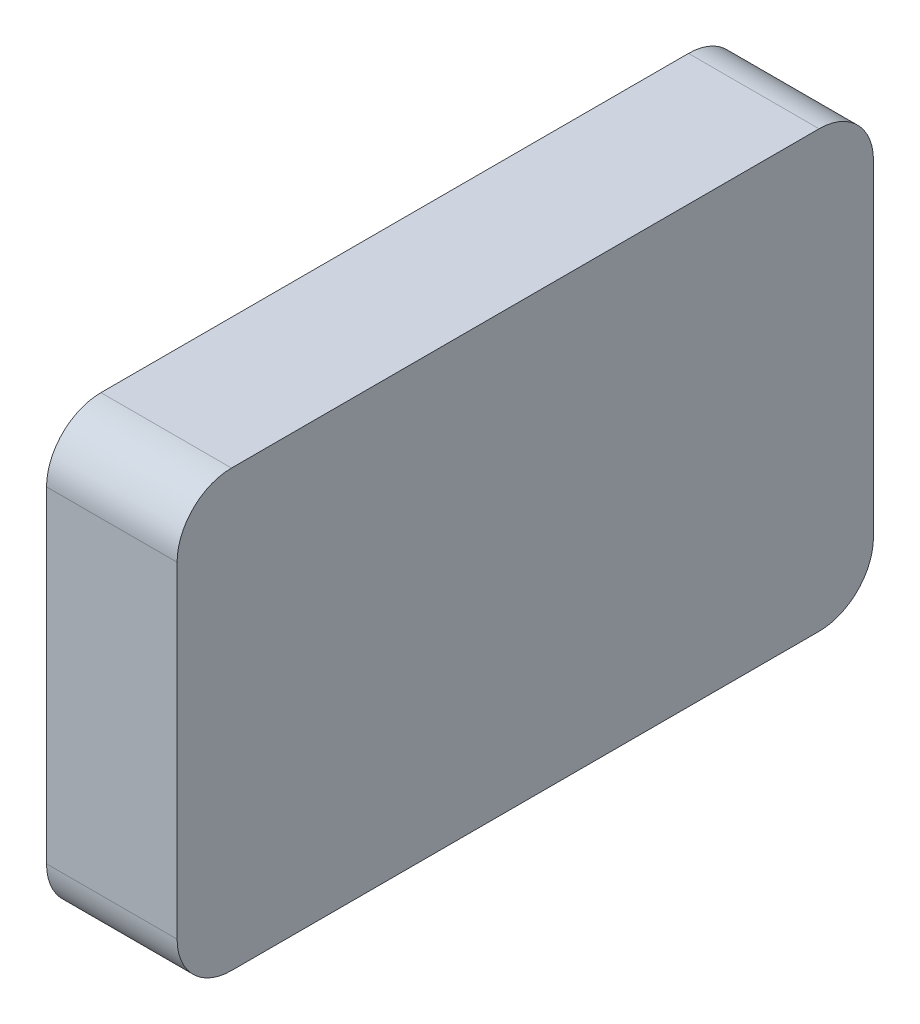
SolidWorks part; units mm, degrees
material "普通碳钢"
ref_plane "前视基准面" through (0, 0, 0) normal (0, 0, 1) x (1, 0, 0)
ref_plane "上视基准面" through (0, 0, 0) normal (0, 1, 0) x (1, 0, 0)
ref_plane "右视基准面" through (0, 0, 0) normal (1, 0, 0) x (0, 0, -1)
sketch "草图1" plane through (0, 0, 0) normal (1, 0, 0) x (0, 0, -1)
  line L1 (-27, 20) -> (27, 20)
  line L2 (-32, 15) -> (-32, -15)
  line L3 (-27, -20) -> (27, -20)
  line L4 (32, 15) -> (32, -15)
  line L5 (-32, 20) -> (32, -20) construction
  line L6 (-32, -20) -> (32, 20) construction
  arc A0 (27, 20) -> (32, 15) centre (27, 15) cw
  arc A1 (27, -20) -> (32, -15) centre (27, -15) ccw
  arc A2 (-27, -20) -> (-32, -15) centre (-27, -15) cw
  arc A3 (-32, 15) -> (-27, 20) centre (-27, 15) cw
  point P0 (0, 0)
  dimension "D3" = 5
  dimension "D1" = 64
  dimension "D2" = 40
extrude "凸台-拉伸1" add sketch "草图1" along normal blind 12
sketch "草图2" plane through (0, 0, 0) normal (-1, 0, 0) x (0, 0, 1)
  circle A1 centre (0, 0) radius 8
  dimension "D1" = 16
extrude "切除-拉伸1" cut sketch "草图2" against normal blind 8 contours A1
sketch "草图3" plane through (0, -20, 0) normal (0, -1, 0) x (1, 0, 0)
  line L0 (0, 0) -> (12, 0) construction
  line L1 (12, 27) -> (12, -27) construction
  circle A0 centre (4, 0) radius 2.5
  dimension "D1" = 5
  dimension "D2" = 4
extrude "切除-拉伸2" cut sketch "草图3" against normal blind 10
